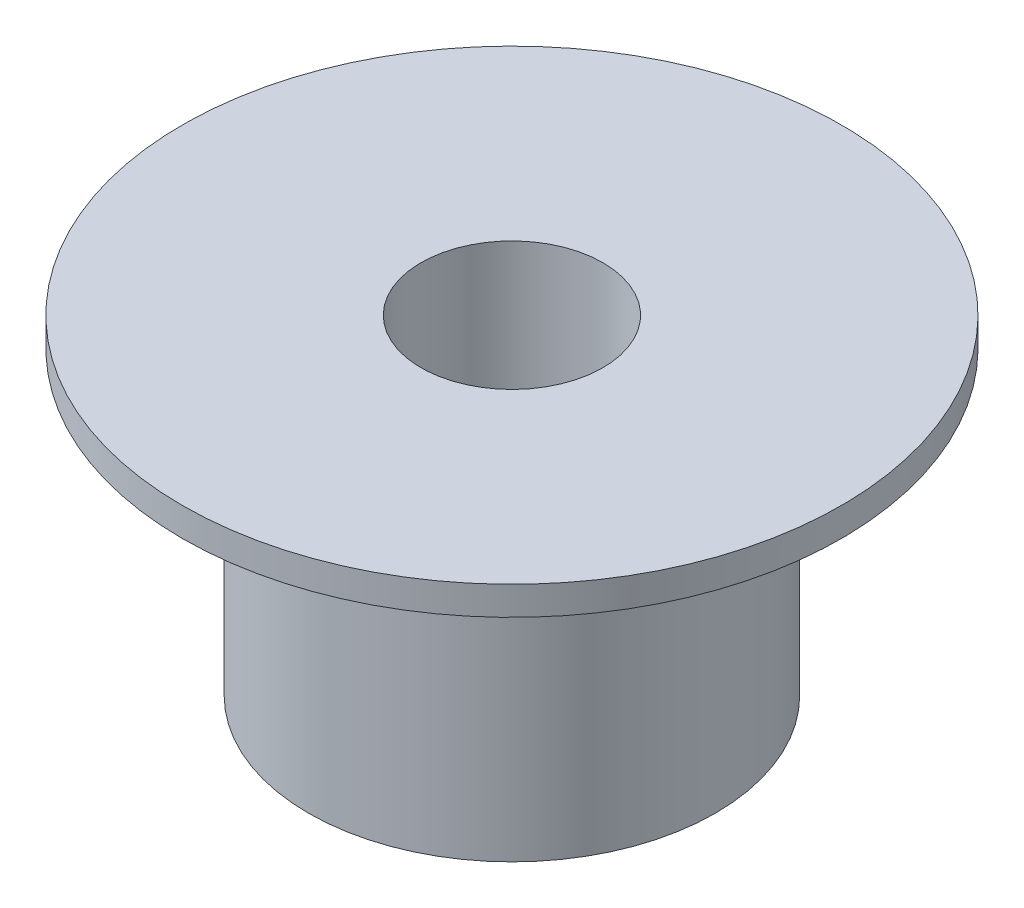
SolidWorks part; units mm, degrees
ref_plane "Front Plane" through (0, 0, 0) normal (0, 0, 1) x (1, 0, 0)
ref_plane "Top Plane" through (0, 0, 0) normal (0, 1, 0) x (1, 0, 0)
ref_plane "Right Plane" through (0, 0, 0) normal (1, 0, 0) x (0, 0, -1)
sketch "Sketch1" plane through (0, 0, 0) normal (0, 1, 0) x (1, 0, 0)
  circle A0 centre (0, 0) radius 7.1
extrude "Boss-Extrude1" add sketch "Sketch1" along normal blind 10.5
sketch "Sketch2" plane through (0, 10.5, 0) normal (0, 1, 0) x (1, 0, 0)
  circle A0 centre (0, 0) radius 11.5
extrude "Boss-Extrude2" add sketch "Sketch2" along normal blind 1
sketch "Sketch3" plane through (0, 0, 0) normal (0, -1, 0) x (1, 0, 0)
  circle A0 centre (0, 0) radius 3.175
extrude "Cut-Extrude1" cut sketch "Sketch3" against normal through all
